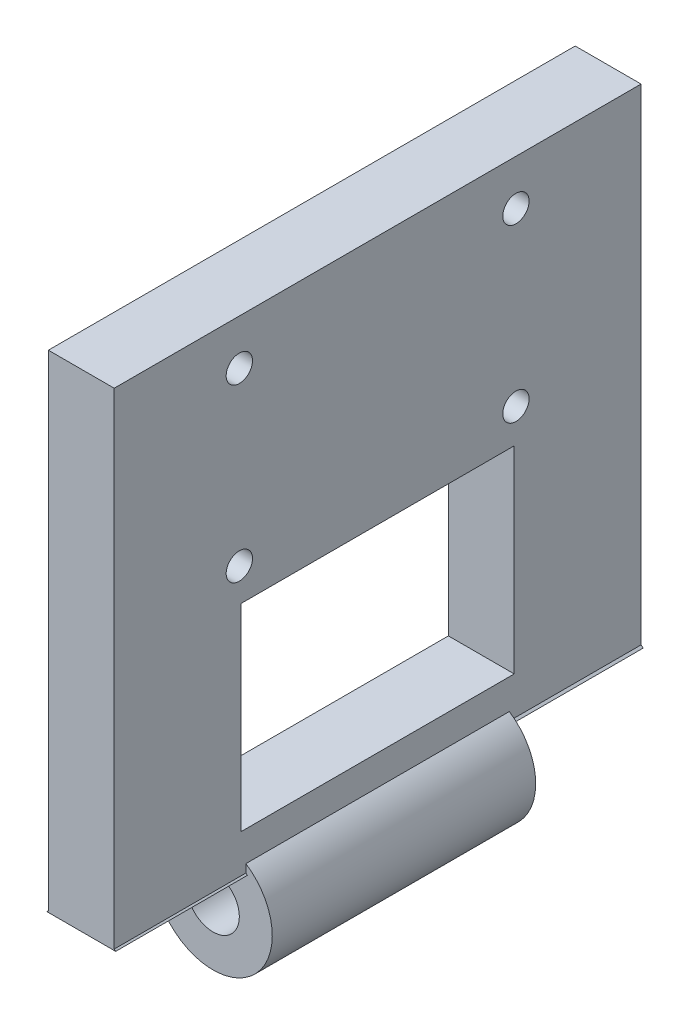
SolidWorks part; units mm, degrees
ref_plane "Front Plane" through (0, 0, 0) normal (0, 0, 1) x (1, 0, 0)
ref_plane "Top Plane" through (0, 0, 0) normal (0, 1, 0) x (1, 0, 0)
ref_plane "Right Plane" through (0, 0, 0) normal (1, 0, 0) x (0, 0, -1)
sketch "Sketch1" plane through (0, 0, 0) normal (1, 0, 0) x (0, 0, -1)
  line L0 (-20, -20) -> (20, -20)
  line L1 (-20, -20) -> (-20, 20)
  line L2 (20, -20) -> (20, 20)
  line L3 (-20, 20) -> (20, 20)
  line L4 (-20, -20) -> (20, 20) construction
  line L5 (20, -20) -> (-20, 20) construction
  point P1 (0, 0)
  dimension "D1" = 40
  dimension "D2" = 40
extrude "Boss-Extrude1" add sketch "Sketch1" along normal blind 5
sketch "Sketch2" plane through (0, 0, 20) normal (0, 0, 1) x (1, 0, 0)
  line L0 (5, -20) -> (0, -20) construction
  circle A0 centre (2.5, -20) radius 1.5
  circle A1 centre (2.5, -20) radius 4
extrude "Boss-Extrude2" add sketch "Sketch2" against normal up to surface (40 mm away) up to face at (2.5, 0, -20)
sketch "Sketch4" plane through (0, 0, 20) normal (0, 0, 1) x (1, 0, 0)
  line L0 (4, -20) -> (1, -20) construction
  circle A0 centre (2.5, -20) radius 1.5
extrude "Cut-Extrude1" cut sketch "Sketch4" against normal up to surface (40 mm away) up to face at (2.5, -20.75, -20)
sketch "Sketch5" plane through (0, 0, -20) normal (0, 0, -1) x (-1, 0, 0)
  line L0 (-7.3228, -25.9889) -> (2.3228, -25.9889)
  line L1 (-7.3228, -25.9889) -> (-7.3228, -17.0111)
  line L2 (2.3228, -25.9889) -> (2.3228, -17.0111)
  line L3 (-7.3228, -17.0111) -> (2.3228, -17.0111)
  line L4 (-7.3228, -25.9889) -> (2.3228, -17.0111) construction
  line L5 (2.3228, -25.9889) -> (-7.3228, -17.0111) construction
  point P1 (-2.5, -21.5)
extrude "Cut-Extrude3" cut sketch "Sketch5" against normal blind 10
sketch "Sketch6" plane through (0, 0, 20) normal (0, 0, 1) x (1, 0, 0)
  line L0 (-4.0941, -31.028) -> (9.0941, -31.028)
  line L1 (-4.0941, -31.028) -> (-4.0941, -16.972)
  line L2 (9.0941, -31.028) -> (9.0941, -16.972)
  line L3 (-4.0941, -16.972) -> (9.0941, -16.972)
  line L4 (-4.0941, -31.028) -> (9.0941, -16.972) construction
  line L5 (9.0941, -31.028) -> (-4.0941, -16.972) construction
  point P1 (2.5, -24)
extrude "Cut-Extrude4" cut sketch "Sketch6" against normal blind 10
sketch "Sketch8" plane through (5, 0, 0) normal (1, 0, 0) x (0, 0, -1)
  line L0 (-20, 1.5612) -> (20, 1.5612) construction
  line L1 (-20, 20) -> (-20, -16.8775) construction
  line L2 (20, -16.8775) -> (20, 20) construction
  line L3 (0, 1.5612) -> (0, 16.5612) construction
  line L4 (0, 16.5612) -> (-10.5, 16.5612) construction
  line L5 (-10.5, 16.5612) -> (-10.5, 10.0612) construction
  line L6 (-10.5, 10.0612) -> (2.3134, 10.0612) construction
  circle A0 centre (-10.5, 16.5612) radius 1
  circle A1 centre (10.5, 16.5612) radius 1
  circle A2 centre (10.5, 3.5612) radius 1
  circle A3 centre (-10.5, 3.5612) radius 1
  point P9 (0, 9.0612)
  dimension "D1" = 10.5
  dimension "D2" = 15
  dimension "D3" = 7.5
  dimension "D4" = 6.5
extrude "Cut-Extrude5" cut sketch "Sketch8" against normal through all
sketch "Sketch9" plane through (5, 0, 0) normal (1, 0, 0) x (0, 0, -1)
  line L0 (-10.3705, -13.9716) -> (-10.3705, 1.0284)
  line L1 (-10.3705, -13.9716) -> (10.3705, -13.9716)
  line L2 (-10.3705, 1.0284) -> (10.3705, 1.0284)
  line L3 (10.3705, -13.9716) -> (10.3705, 1.0284)
  line L4 (-10.3705, -13.9716) -> (10.3705, 1.0284) construction
  line L5 (-10.3705, 1.0284) -> (10.3705, -13.9716) construction
  point P1 (0, -6.4716)
  dimension "D1" = 15
extrude "Cut-Extrude6" cut sketch "Sketch9" against normal through all
sketch "Sketch13" plane through (5, 0, 0) normal (1, 0, 0) x (0, 0, -1)
  point P0 (-10.3705, -13.9716)
  point P1 (-10.3705, 1.0284)
  point P3 (10.3705, 1.0284)
  point P5 (10, -17.0111)
  point P7 (-10, -16.972)
  dimension "D1" = 20.741
  dimension "D2" = 15
ref_plane "Plane8" through (5, -13.9716, 10.3705) normal (0, -1, 0) x (-1, 0, 0)
sketch "Sketch15" plane through (5, 0, 0) normal (1, 0, 0) x (0, 0, -1)
  line L0 (-10, -16.972) -> (-10, -24) construction
  point P0 (10.3705, 1.0284)
  point P1 (-20, -16.972)
  point P3 (-10.3705, -13.9716)
  point P4 (-20, 20)
  point P8 (10, -17.0111)
  point P13 (20, 20)
  dimension "D1" = 15
  dimension "D2" = 20.741
  dimension "D3" = 36.972
  dimension "D4" = 20
  dimension "D5" = 40
sketch "Sketch16" plane through (0, 0, 10) normal (0, 0, 1) x (1, 0, 0)
  circle A0 centre (2.5, -20) radius 4.5
extrude "Boss-Extrude3" add sketch "Sketch16" against normal blind 20
sketch "Sketch17" plane through (0, 0, 10) normal (0, 0, 1) x (1, 0, 0)
  circle A0 centre (2.5, -20) radius 2
extrude "Cut-Extrude7" cut sketch "Sketch17" against normal blind 20
